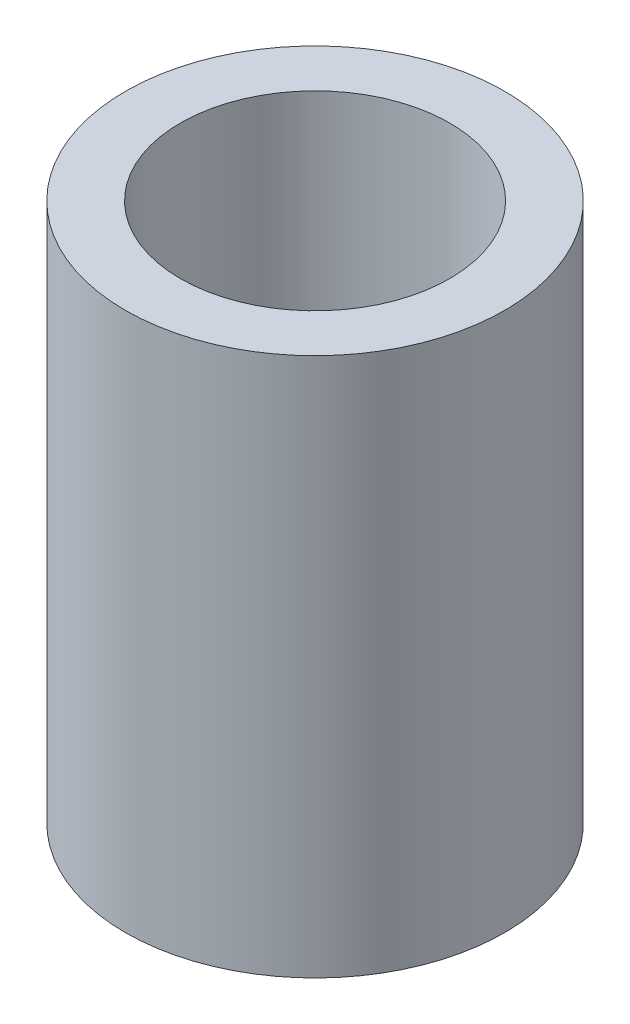
SolidWorks part; units mm, degrees
material "ABS"
ref_plane "Front Plane" through (0, 0, 0) normal (0, 0, 1) x (1, 0, 0)
ref_plane "Top Plane" through (0, 0, 0) normal (0, 1, 0) x (1, 0, 0)
ref_plane "Right Plane" through (0, 0, 0) normal (1, 0, 0) x (0, 0, -1)
sketch "Sketch1" plane through (0, 0, 0) normal (0, 1, 0) x (1, 0, 0)
  circle A0 centre (0, 0) radius 3.9688
  circle A1 centre (0, 0) radius 5.588
  dimension "D1" = 7.9375
  dimension "D2" = 11.176
extrude "Boss-Extrude1" add sketch "Sketch1" along normal blind 15.875
